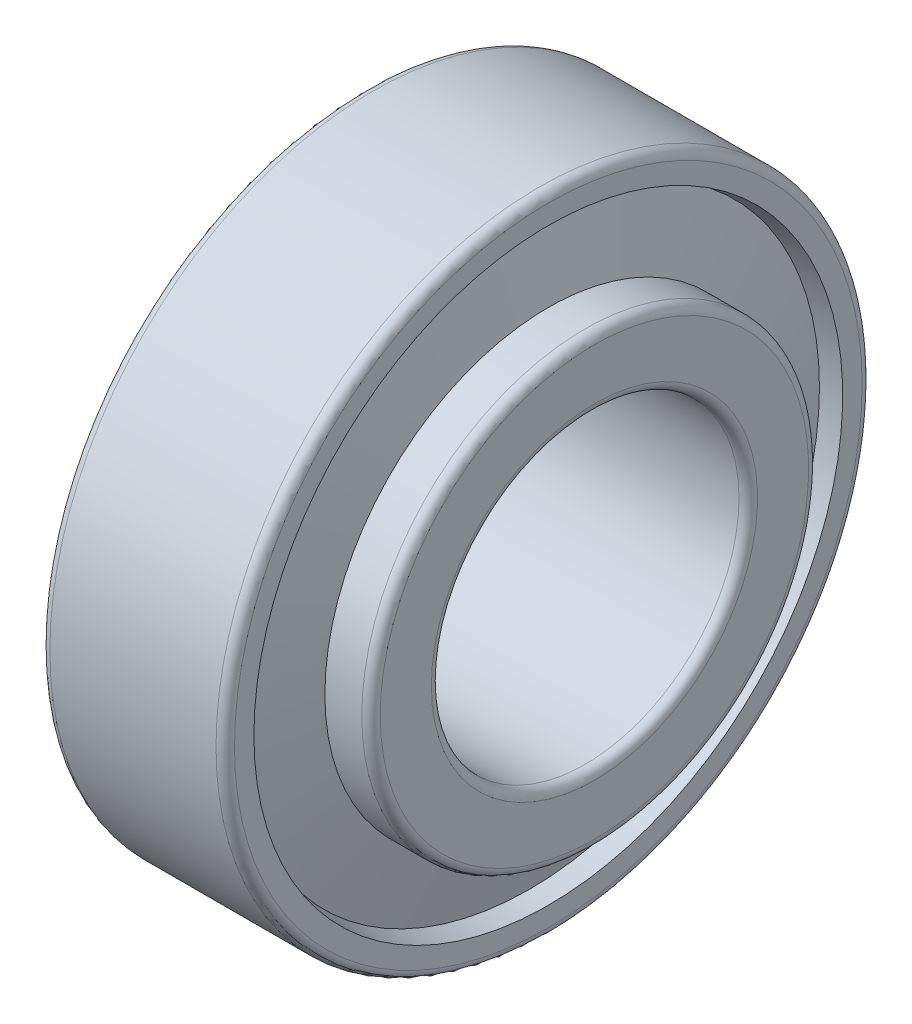
SolidWorks part; units mm, degrees
material "AISI Тип A2 Инструментальная сталь"
ref_plane "Спереди" through (0, 0, 0) normal (0, 0, 1) x (1, 0, 0)
ref_plane "Сверху" through (0, 0, 0) normal (0, 1, 0) x (1, 0, 0)
ref_plane "Справа" through (0, 0, 0) normal (1, 0, 0) x (0, 0, -1)
sketch "Эскиз1" plane through (0, 0, 0) normal (0, 0, 1) x (1, 0, 0)
  line L20 (-882.5277, 0) -> (43243.8573, 0) construction
  line L33 (1.32, 16.6928) -> (0, 16.3905)
  line L34 (0, 16.3905) -> (0, 20.4)
  line L35 (0.6, 21) -> (11.4, 21)
  line L36 (12, 20.4) -> (12, 19.1384)
  line L37 (12, 19.1384) -> (10.7702, 18.8567)
  line L38 (1.32, 16.6928) -> (10.7702, 18.8567) construction
  line L39 (2.6401, 11.3984) -> (0, 11.3984)
  line L40 (0, 11.3984) -> (0, 10.6)
  line L41 (0.6, 10) -> (14.4, 10)
  line L42 (15, 10.6) -> (15, 13.9243)
  line L43 (14.4, 14.5243) -> (12, 14.5243)
  line L44 (12, 14.5243) -> (12, 13.9243)
  line L45 (2.6401, 11.3984) -> (12, 13.9243) construction
  line L46 (12, 13.9243) -> (10.7702, 18.8567)
  line L47 (2.6401, 11.3984) -> (1.32, 16.6928)
  line L48 (1.9801, 14.0456) -> (11.3851, 16.3905) construction
  line L49 (0, 16.3905) -> (11.3851, 16.3905) construction
  line L50 (1.32, 16.6928) -> (1.32, 11.3984) construction
  arc A0 (0, 20.4) -> (0.6, 21) centre (0.6, 20.4) cw
  arc A1 (11.4, 21) -> (12, 20.4) centre (11.4, 20.4) cw
  arc A2 (0, 10.6) -> (0.6, 10) centre (0.6, 10.6) ccw
  arc A3 (15, 10.6) -> (14.4, 10) centre (14.4, 10.6) cw
  arc A4 (14.4, 14.5243) -> (15, 13.9243) centre (14.4, 13.9243) cw
  point P12 (11.3851, 16.3905)
  dimension "гост r1" = 0.6
  dimension "гост r2" = 0.6
  dimension "гост DD" = 42
  dimension "гост B" = 15
  dimension "гост C" = 12
  dimension "гост T" = 15
  dimension "гост E" = 32.781
  dimension "гост d" = 20
  dimension "гост alfa" = 14
revolve "Повернуть1" add sketch "Эскиз1" angle 360 about L20
